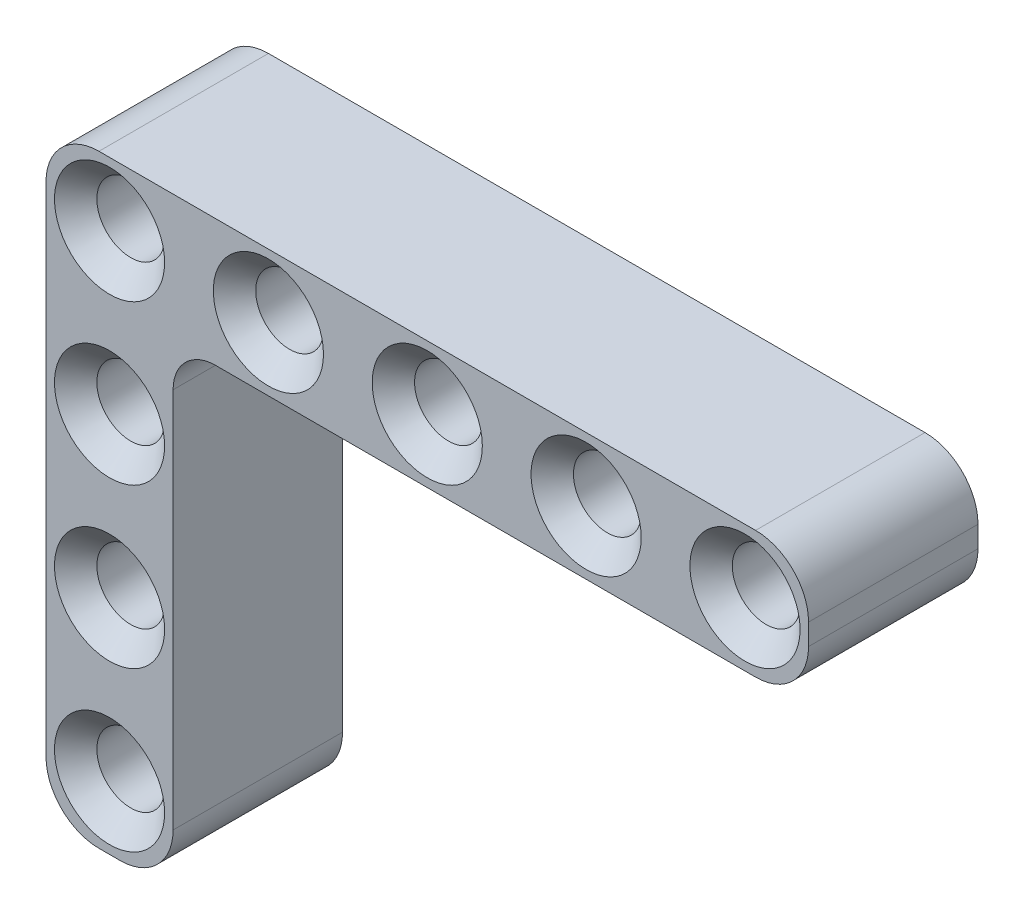
SolidWorks part; units mm, degrees
ref_plane "Front Plane" through (0, 0, 0) normal (0, 0, 1) x (1, 0, 0)
ref_plane "Top Plane" through (0, 0, 0) normal (0, 1, 0) x (1, 0, 0)
ref_plane "Right Plane" through (0, 0, 0) normal (1, 0, 0) x (0, 0, -1)
sketch "Sketch1" plane through (0, 0, 0) normal (0, 0, 1) x (1, 0, 0)
  line L1 (-0.5, 3) -> (30.5, 3)
  line L2 (-3, 0.5) -> (-3, -0.5)
  line L3 (-0.5, -3) -> (30.5, -3)
  line L4 (33, 0.5) -> (33, -0.5)
  circle A0 centre (0, 0) radius 1.6
  arc A1 (30.5, -3) -> (33, -0.5) centre (30.5, -0.5) ccw
  arc A2 (30.5, 3) -> (33, 0.5) centre (30.5, 0.5) cw
  arc A3 (-3, -0.5) -> (-0.5, -3) centre (-0.5, -0.5) ccw
  arc A4 (-0.5, 3) -> (-3, 0.5) centre (-0.5, 0.5) ccw
  circle A5 centre (7.5, 0) radius 1.6
  circle A6 centre (15, 0) radius 1.6
  circle A7 centre (22.5, 0) radius 1.6
  circle A8 centre (30, 0) radius 1.6
  point P8 (-3, 0)
  point P14 (-3, -3)
  point P17 (-3, 3)
  dimension "D1" = 3.2
  dimension "D4" = 2.5
  dimension "D2" = 6
  dimension "D3" = 3
  dimension "D6" = 7.5
  dimension "D5" = 5
extrude "Boss-Extrude1" add sketch "Sketch1" along normal blind 8
chamfer "Chamfer1" distance 1 angle 45 10 edges at (31.6, 0, 0) (31.6, 0, 8) (24.1, 0, 0) (24.1, 0, 8) (16.6, 0, 0) (16.6, 0, 8) (9.1, 0, 0) (9.1, 0, 8) (1.6, 0, 0) (1.6, 0, 8)
sketch "Sketch2" plane through (0, 0, 8) normal (0, 0, 1) x (1, 0, 0)
  line L0 (-3, 0) -> (-3, -23)
  line L1 (-0.5, -25.5) -> (0.5, -25.5)
  line L2 (3, -23) -> (3, -3)
  line L3 (-3, 0.5) -> (-3, -0.5) construction
  line L4 (-0.5, -3) -> (30.5, -3) construction
  circle A1 centre (0, -7.5) radius 1.6
  arc A4 (-3, -23) -> (-0.5, -25.5) centre (-0.5, -23) ccw
  arc A5 (0.5, -25.5) -> (3, -23) centre (0.5, -23) ccw
  circle A6 centre (0, -15) radius 1.6
  circle A7 centre (0, -22.5) radius 1.6
  point P18 (-3, -25.5)
  point P21 (3, -25.5)
  dimension "D3" = 3.2
  dimension "D8" = 2.5
  dimension "D1" = 6
  dimension "D2" = 90
  dimension "D4" = 3
  dimension "D5" = 7.5
  dimension "D7" = 3
  dimension "D6" = 3
extrude "Boss-Extrude3" add sketch "Sketch2" against normal blind 8
fillet "Fillet1" radius 2 1 edges at (3, -3, 4)
chamfer "Chamfer5" distance 1 angle 45 6 edges at (1.6, -7.5, 8) (1.6, -7.5, 0) (1.6, -15, 8) (1.6, -15, 0) (1.6, -22.5, 8) (1.6, -22.5, 0)
